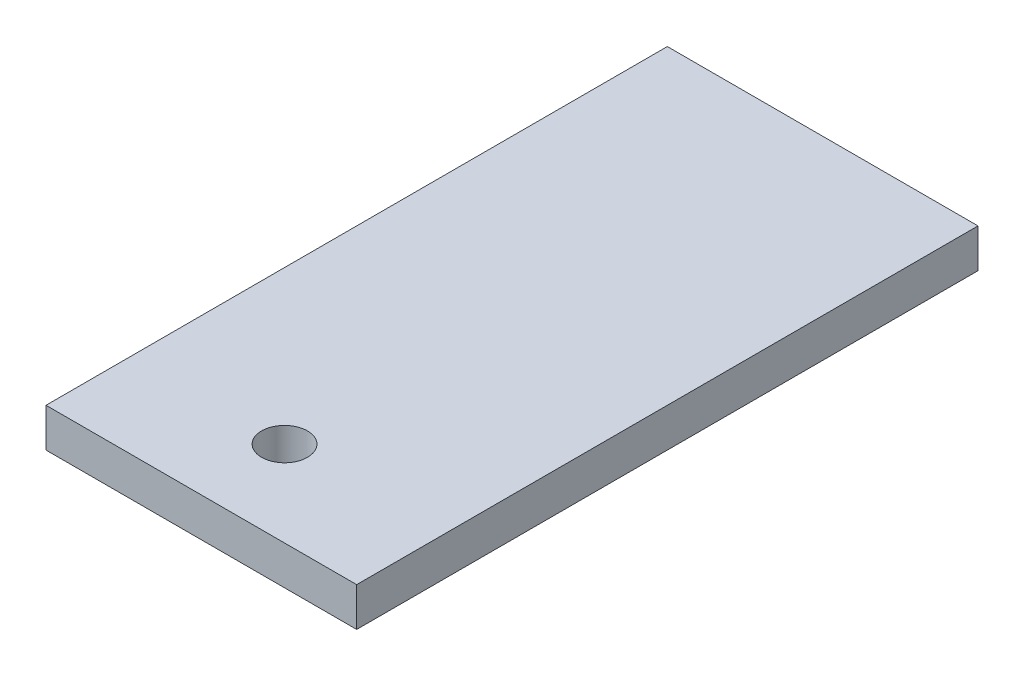
SolidWorks part; units mm, degrees
ref_plane "Front Plane" through (0, 0, 0) normal (0, 0, 1) x (1, 0, 0)
ref_plane "Top Plane" through (0, 0, 0) normal (0, 1, 0) x (1, 0, 0)
ref_plane "Right Plane" through (0, 0, 0) normal (1, 0, 0) x (0, 0, -1)
sketch "Sketch1" plane through (0, 0, 0) normal (0, 1, 0) x (1, 0, 0)
  line L1 (0, 0) -> (203.2, 0)
  line L2 (0, 0) -> (0, 406.4)
  line L3 (0, 406.4) -> (203.2, 406.4)
  line L4 (203.2, 0) -> (203.2, 406.4)
  dimension "D1" = 203.2
  dimension "D2" = 406.4
extrude "Boss-Extrude1" add sketch "Sketch1" along normal blind 25.4
sketch "Sketch3" plane through (0, 25.4, 0) normal (0, 1, 0) x (1, 0, 0)
  line L1 (0, 406.4) -> (100, 406.4)
  line L2 (0, 406.4) -> (0, 56)
  line L3 (0, 56) -> (100, 56)
  line L4 (100, 406.4) -> (100, 56)
  circle A0 centre (100, 56) radius 15
  dimension "D1" = 350.4
  dimension "D2" = 100
extrude "Cut-Extrude2" cut sketch "Sketch3" against normal blind 25.4 contours A0
